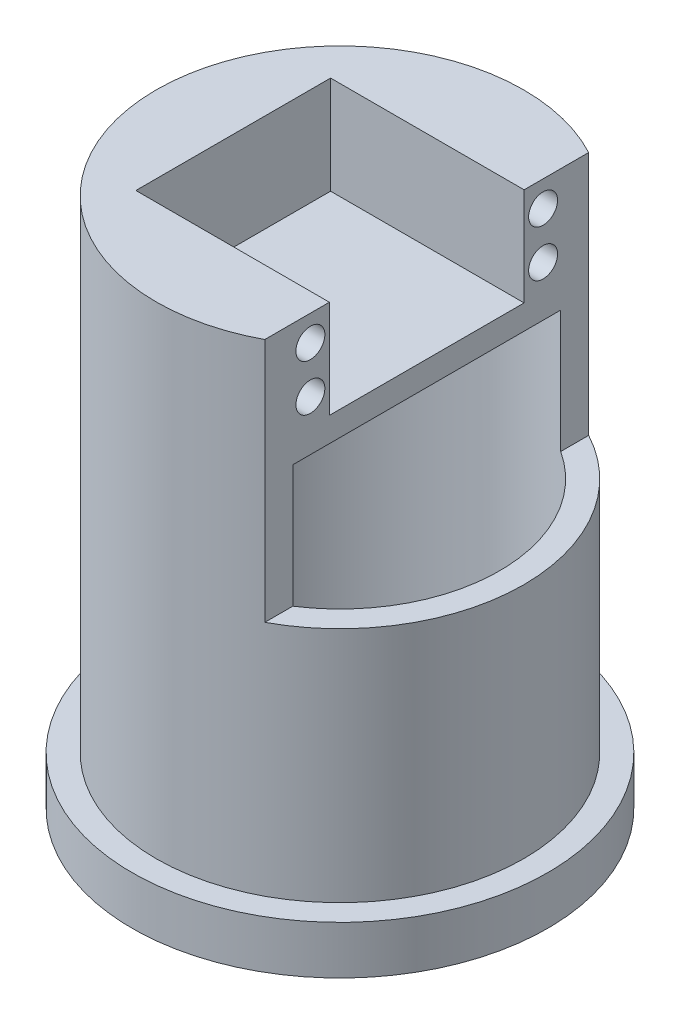
SolidWorks part; units mm, degrees
material "ABS"
ref_plane "Front Plane" through (0, 0, 0) normal (0, 0, 1) x (1, 0, 0)
ref_plane "Top Plane" through (0, 0, 0) normal (0, 1, 0) x (1, 0, 0)
ref_plane "Right Plane" through (0, 0, 0) normal (1, 0, 0) x (0, 0, -1)
sketch "Sketch1" plane through (0, 0, 0) normal (0, 1, 0) x (1, 0, 0)
  circle A0 centre (0, 0) radius 38.1
  dimension "D1" = 76.2
extrude "Boss-Extrude1" add sketch "Sketch1" along normal blind 100
shell "Shell1" thickness 5
sketch "Sketch2" plane through (0, 0, 0) normal (0, -1, 0) x (1, 0, 0)
  circle A0 centre (0, 0) radius 43.1
  circle A1 centre (0, 0) radius 33.1
  circle A2 centre (0, 0) radius 33.1 construction
  dimension "D1" = 10
extrude "Boss-Extrude2" add sketch "Sketch2" along normal blind 10
ref_plane "Plane1" through (0, 0, 33.1) normal (0, 0, -1) x (-1, 0, 0)
sketch "Sketch4" plane through (0, -10, 0) normal (0, -1, 0) x (1, 0, 0)
  line L0 (0, 33.1) -> (0, -33.1) construction
  line L1 (-13, 30.4403) -> (-13, -30.4403) construction
  circle A0 centre (0, 0) radius 33.1 construction
  arc A1 (-13, 30.4403) -> (-13, -30.4403) centre (-70, 0) cw
  arc A2 (13, 30.4403) -> (13, -30.4403) centre (70, 0) ccw
  arc A3 (-13, 30.4403) -> (13, 30.4403) centre (0, 0) cw
  arc A4 (13, -30.4403) -> (-13, -30.4403) centre (0, 0) cw
  dimension "D2" = 70
  dimension "D1" = 13
extrude "Boss-Extrude3" add sketch "Sketch4" against normal blind 5
sketch "Sketch5" plane through (0, -10, 0) normal (0, -1, 0) x (1, 0, 0)
  line L0 (-2, 1.5) -> (2, 1.5) construction
  line L1 (-2, -1.5) -> (2, -1.5) construction
  line L2 (-2, 1.5) -> (2, 1.5) construction
  line L3 (-2, 1.5) -> (2, 1.5)
  line L4 (-2, -1.5) -> (2, -1.5)
  arc A1 (-2, 1.5) -> (-2, -1.5) centre (0, 0) ccw
  arc A2 (2, -1.5) -> (2, 1.5) centre (0, 0) ccw
  dimension "D2" = 3
  dimension "D1" = 5
extrude "Cut-Extrude1" cut sketch "Sketch5" against normal blind 5
sketch "Sketch6" plane through (0, 100, 0) normal (0, 1, 0) x (1, 0, 0)
  line L2 (18, 33.5799) -> (18, -33.5799)
  arc A6 (18, 33.5799) -> (18, -33.5799) centre (0, 0) ccw
  circle A7 centre (0, 0) radius 38.1 construction
  circle A9 centre (0, 0) radius 38.1 construction
  point P3 (18.0541, 33.5509)
  dimension "D1" = 18
extrude "Boss-Extrude4" add sketch "Sketch6" against normal blind 25.4
sketch "Sketch8" plane through (0, 100, 0) normal (0, 1, 0) x (1, 0, 0)
  line L0 (18, -42.9553) -> (18, 42.9553)
  arc A0 (18, 42.9553) -> (18, -42.9553) centre (8.2166, 0) cw
  point P3 (18, 0)
extrude "Cut-Extrude3" cut sketch "Sketch8" against normal blind 50.8
sketch "Sketch9" plane through (18, 0, 0) normal (1, 0, 0) x (0, 0, -1)
  line L0 (0, 100) -> (0, 0) construction
  line L1 (-33.5799, 100) -> (33.5799, 100) construction
  line L2 (-24.13, 89.84) -> (24.13, 89.84) construction
  line L3 (-24.13, 85.014) -> (-24.13, 94.666) construction
  line L5 (-20.193, 79.68) -> (20.193, 79.68)
  line L6 (-20.193, 79.68) -> (-20.193, 100)
  line L7 (-20.193, 100) -> (20.193, 100)
  line L8 (20.193, 79.68) -> (20.193, 100)
  line L9 (-20.193, 79.68) -> (20.193, 100) construction
  line L10 (-20.193, 100) -> (20.193, 79.68) construction
  circle A0 centre (-24.13, 94.666) radius 3
  circle A1 centre (-24.13, 85.014) radius 3
  circle A2 centre (24.13, 85.014) radius 3
  circle A3 centre (24.13, 94.666) radius 3
  point P8 (0, 89.84)
  point P11 (-24.13, 89.84)
  point P17 (0, 89.84)
  dimension "D4" = 6
  dimension "D1" = 48.26
  dimension "D2" = 10.16
  dimension "D3" = 9.652
  dimension "D5" = 40.386
extrude "Cut-Extrude4" cut sketch "Sketch9" against normal blind 40.132
